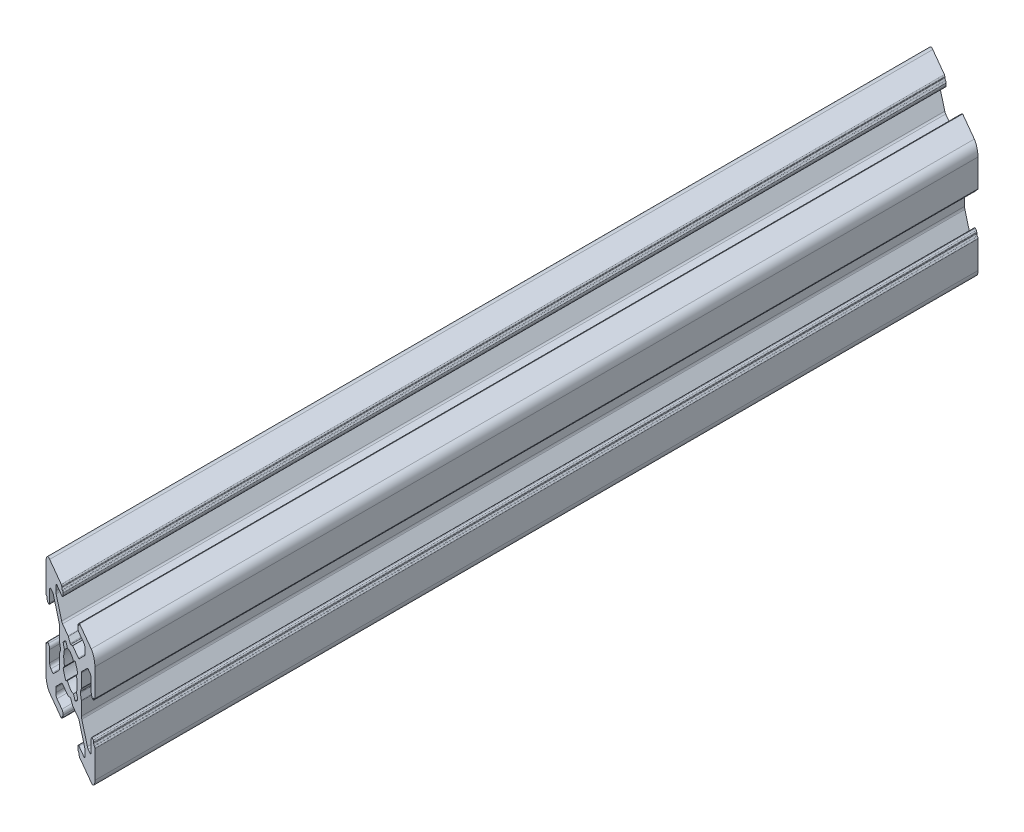
SolidWorks part; units mm, degrees
ref_plane "Front Plane" through (0, 0, 0) normal (0, 0, 1) x (1, 0, 0)
ref_plane "Top Plane" through (0, 0, 0) normal (0, 1, 0) x (1, 0, 0)
ref_plane "Right Plane" through (0, 0, 0) normal (1, 0, 0) x (0, 0, -1)
sketch "Sketch1" plane through (0, 0, 0) normal (0, 0, 1) x (1, 0, 0)
  line L0 (0, 13.3675) -> (0, -10.9159) construction
  line L1 (-12.9725, 0) -> (15.1887, 0) construction
  line L2 (-3.5, 8.5) -> (-5.5, 8.5)
  line L3 (-3.55, 9.7) -> (-3.55, 9.8)
  line L4 (-6, 7.2678) -> (-6, 8)
  line L5 (-7.2678, 6) -> (-8, 6)
  line L6 (-3.75, 10) -> (-8.5, 10)
  line L7 (-9.7, 3.55) -> (-9.8, 3.55)
  line L8 (-9.5, 3.2) -> (-9.5, 3.35)
  line L9 (-9, 3) -> (-9.3, 3)
  line L10 (-4.4732, 0.8536) -> (-4.0381, 0.1)
  line L11 (-4.5, 3.2322) -> (-4.5, 0.9536)
  line L12 (-8.5, 3.5) -> (-8.5, 5.5)
  line L13 (-10, 3.75) -> (-10, 8.5)
  line L14 (-3.5858, 4.6464) -> (-5.8536, 6.9142)
  line L15 (-4.6464, 3.5858) -> (-6.9142, 5.8536)
  line L16 (-3.2, 9.5) -> (-3.35, 9.5)
  line L17 (-3, 9) -> (-3, 9.3)
  line L18 (-0.8536, 4.4732) -> (-0.1, 4.0381)
  line L19 (-3.2322, 4.5) -> (-0.9536, 4.5)
  line L20 (-1.2582, 2.4453) -> (-1.9139, 2.9896)
  line L21 (-2.4453, 1.2582) -> (-2.9922, 1.9099)
  line L22 (3.5, -8.5) -> (5.5, -8.5)
  line L23 (3.55, -9.7) -> (3.55, -9.8)
  line L24 (6, -7.2678) -> (6, -8)
  line L25 (7.2678, -6) -> (8, -6)
  line L26 (3.75, -10) -> (8.5, -10)
  line L27 (9.7, -3.55) -> (9.8, -3.55)
  line L28 (9.5, -3.2) -> (9.5, -3.35)
  line L29 (9, -3) -> (9.3, -3)
  line L30 (4.4732, -0.8536) -> (4.0381, -0.1)
  line L31 (4.5, -3.2322) -> (4.5, -0.9536)
  line L32 (8.5, -3.5) -> (8.5, -5.5)
  line L33 (10, -3.75) -> (10, -8.5)
  line L34 (3.5858, -4.6464) -> (5.8536, -6.9142)
  line L35 (4.6464, -3.5858) -> (6.9142, -5.8536)
  line L36 (3.2, -9.5) -> (3.35, -9.5)
  line L37 (3, -9) -> (3, -9.3)
  line L38 (0.8536, -4.4732) -> (0.1, -4.0381)
  line L39 (3.2322, -4.5) -> (0.9536, -4.5)
  line L40 (1.2582, -2.4453) -> (1.9139, -2.9896)
  line L41 (2.4453, -1.2582) -> (2.9922, -1.9099)
  line L42 (-2.4453, -1.2582) -> (-2.9922, -1.9099)
  line L43 (-1.2582, -2.4453) -> (-1.9139, -2.9896)
  line L44 (-3.2322, -4.5) -> (-0.9536, -4.5)
  line L45 (-0.8536, -4.4732) -> (-0.1, -4.0381)
  line L46 (-3, -9) -> (-3, -9.3)
  line L47 (-3.2, -9.5) -> (-3.35, -9.5)
  line L48 (-4.6464, -3.5858) -> (-6.9142, -5.8536)
  line L49 (-3.5858, -4.6464) -> (-5.8536, -6.9142)
  line L50 (-10, -3.75) -> (-10, -8.5)
  line L51 (-8.5, -3.5) -> (-8.5, -5.5)
  line L52 (-4.5, -3.2322) -> (-4.5, -0.9536)
  line L53 (-4.4732, -0.8536) -> (-4.0381, -0.1)
  line L54 (-9, -3) -> (-9.3, -3)
  line L55 (-9.5, -3.2) -> (-9.5, -3.35)
  line L56 (-9.7, -3.55) -> (-9.8, -3.55)
  line L57 (2.4453, 1.2582) -> (2.9922, 1.9099)
  line L58 (1.2582, 2.4453) -> (1.9139, 2.9896)
  line L59 (3.2322, 4.5) -> (0.9536, 4.5)
  line L60 (0.8536, 4.4732) -> (0.1, 4.0381)
  line L61 (-3.75, -10) -> (-8.5, -10)
  line L62 (-7.2678, -6) -> (-8, -6)
  line L63 (-6, -7.2678) -> (-6, -8)
  line L64 (3, 9) -> (3, 9.3)
  line L65 (3.2, 9.5) -> (3.35, 9.5)
  line L66 (4.6464, 3.5858) -> (6.9142, 5.8536)
  line L67 (3.5858, 4.6464) -> (5.8536, 6.9142)
  line L68 (10, 3.75) -> (10, 8.5)
  line L69 (8.5, 3.5) -> (8.5, 5.5)
  line L70 (4.5, 3.2322) -> (4.5, 0.9536)
  line L71 (4.4732, 0.8536) -> (4.0381, 0.1)
  line L72 (9, 3) -> (9.3, 3)
  line L73 (9.5, 3.2) -> (9.5, 3.35)
  line L74 (9.7, 3.55) -> (9.8, 3.55)
  line L75 (3.75, 10) -> (8.5, 10)
  line L76 (7.2678, 6) -> (8, 6)
  line L77 (6, 7.2678) -> (6, 8)
  line L78 (3.55, 9.7) -> (3.55, 9.8)
  line L79 (3.5, 8.5) -> (5.5, 8.5)
  line L80 (-3.55, -9.7) -> (-3.55, -9.8)
  line L81 (-3.5, -8.5) -> (-5.5, -8.5)
  arc A0 (-10, 8.5) -> (-8.5, 10) centre (-8.5, 8.5) cw
  arc A1 (-8.5, 5.5) -> (-8, 6) centre (-8, 5.5) cw
  arc A2 (-7.2678, 6) -> (-6.9142, 5.8536) centre (-7.2678, 5.5) cw
  arc A3 (-5.8536, 6.9142) -> (-6, 7.2678) centre (-5.5, 7.2678) cw
  arc A4 (-6, 8) -> (-5.5, 8.5) centre (-5.5, 8) cw
  arc A5 (-9.7, 3.55) -> (-9.5, 3.35) centre (-9.7, 3.35) cw
  arc A6 (-9.8, 3.55) -> (-10, 3.75) centre (-9.8, 3.75) cw
  arc A7 (-9.3, 3) -> (-9.5, 3.2) centre (-9.3, 3.2) cw
  arc A8 (-8.5, 3.5) -> (-9, 3) centre (-9, 3.5) cw
  arc A9 (-4.6464, 3.5858) -> (-4.5, 3.2322) centre (-5, 3.2322) cw
  arc A10 (-4.4732, 0.8536) -> (-4.5, 0.9536) centre (-4.3, 0.9536) cw
  arc A11 (-4.0381, 0.1) -> (-4.0381, -0.1) centre (-4.2113, 0) cw
  arc A12 (-3.2, 9.5) -> (-3, 9.3) centre (-3.2, 9.3) cw
  arc A13 (-0.9536, 4.5) -> (-0.8536, 4.4732) centre (-0.9536, 4.3) cw
  arc A14 (-2.9922, 1.9099) -> (-1.9139, 2.9896) centre (0, 0) cw
  arc A15 (-3.2322, 4.5) -> (-3.5858, 4.6464) centre (-3.2322, 5) cw
  arc A16 (-3.75, 10) -> (-3.55, 9.8) centre (-3.75, 9.8) cw
  arc A17 (-3.35, 9.5) -> (-3.55, 9.7) centre (-3.35, 9.7) cw
  arc A18 (2.4453, -1.2582) -> (2.4453, 1.2582) centre (0, 0) ccw
  arc A19 (-3, 9) -> (-3.5, 8.5) centre (-3.5, 9) cw
  arc A20 (-2.4453, -1.2582) -> (-2.4453, 1.2582) centre (0, 0) cw
  arc A21 (10, -8.5) -> (8.5, -10) centre (8.5, -8.5) cw
  arc A22 (8.5, -5.5) -> (8, -6) centre (8, -5.5) cw
  arc A23 (7.2678, -6) -> (6.9142, -5.8536) centre (7.2678, -5.5) cw
  arc A24 (5.8536, -6.9142) -> (6, -7.2678) centre (5.5, -7.2678) cw
  arc A25 (6, -8) -> (5.5, -8.5) centre (5.5, -8) cw
  arc A26 (9.7, -3.55) -> (9.5, -3.35) centre (9.7, -3.35) cw
  arc A27 (9.8, -3.55) -> (10, -3.75) centre (9.8, -3.75) cw
  arc A28 (9.3, -3) -> (9.5, -3.2) centre (9.3, -3.2) cw
  arc A29 (8.5, -3.5) -> (9, -3) centre (9, -3.5) cw
  arc A30 (4.6464, -3.5858) -> (4.5, -3.2322) centre (5, -3.2322) cw
  arc A31 (4.4732, -0.8536) -> (4.5, -0.9536) centre (4.3, -0.9536) cw
  arc A32 (3.2, -9.5) -> (3, -9.3) centre (3.2, -9.3) cw
  arc A33 (-0.1, -4.0381) -> (0.1, -4.0381) centre (0, -4.2113) cw
  arc A34 (0.9536, -4.5) -> (0.8536, -4.4732) centre (0.9536, -4.3) cw
  arc A35 (2.9922, -1.9099) -> (1.9139, -2.9896) centre (0, 0) cw
  arc A36 (1.2582, -2.4453) -> (-1.2582, -2.4453) centre (0, 0) cw
  arc A37 (3.2322, -4.5) -> (3.5858, -4.6464) centre (3.2322, -5) cw
  arc A38 (3.75, -10) -> (3.55, -9.8) centre (3.75, -9.8) cw
  arc A39 (3.35, -9.5) -> (3.55, -9.7) centre (3.35, -9.7) cw
  arc A40 (3, -9) -> (3.5, -8.5) centre (3.5, -9) cw
  arc A41 (-3, -9) -> (-3.5, -8.5) centre (-3.5, -9) ccw
  arc A42 (-3.35, -9.5) -> (-3.55, -9.7) centre (-3.35, -9.7) ccw
  arc A43 (-3.75, -10) -> (-3.55, -9.8) centre (-3.75, -9.8) ccw
  arc A44 (-3.2322, -4.5) -> (-3.5858, -4.6464) centre (-3.2322, -5) ccw
  arc A45 (-2.9922, -1.9099) -> (-1.9139, -2.9896) centre (0, 0) ccw
  arc A46 (-0.9536, -4.5) -> (-0.8536, -4.4732) centre (-0.9536, -4.3) ccw
  arc A47 (-3.2, -9.5) -> (-3, -9.3) centre (-3.2, -9.3) ccw
  arc A48 (-4.4732, -0.8536) -> (-4.5, -0.9536) centre (-4.3, -0.9536) ccw
  arc A49 (3, 9) -> (3.5, 8.5) centre (3.5, 9) ccw
  arc A50 (3.35, 9.5) -> (3.55, 9.7) centre (3.35, 9.7) ccw
  arc A51 (3.75, 10) -> (3.55, 9.8) centre (3.75, 9.8) ccw
  arc A52 (3.2322, 4.5) -> (3.5858, 4.6464) centre (3.2322, 5) ccw
  arc A53 (1.2582, 2.4453) -> (-1.2582, 2.4453) centre (0, 0) ccw
  arc A54 (-4.6464, -3.5858) -> (-4.5, -3.2322) centre (-5, -3.2322) ccw
  arc A55 (-8.5, -3.5) -> (-9, -3) centre (-9, -3.5) ccw
  arc A56 (-9.3, -3) -> (-9.5, -3.2) centre (-9.3, -3.2) ccw
  arc A57 (-9.8, -3.55) -> (-10, -3.75) centre (-9.8, -3.75) ccw
  arc A58 (-9.7, -3.55) -> (-9.5, -3.35) centre (-9.7, -3.35) ccw
  arc A59 (-6, -8) -> (-5.5, -8.5) centre (-5.5, -8) ccw
  arc A60 (2.9922, 1.9099) -> (1.9139, 2.9896) centre (0, 0) ccw
  arc A61 (0.9536, 4.5) -> (0.8536, 4.4732) centre (0.9536, 4.3) ccw
  arc A62 (-0.1, 4.0381) -> (0.1, 4.0381) centre (0, 4.2113) ccw
  arc A63 (-5.8536, -6.9142) -> (-6, -7.2678) centre (-5.5, -7.2678) ccw
  arc A64 (-7.2678, -6) -> (-6.9142, -5.8536) centre (-7.2678, -5.5) ccw
  arc A65 (-8.5, -5.5) -> (-8, -6) centre (-8, -5.5) ccw
  arc A66 (-10, -8.5) -> (-8.5, -10) centre (-8.5, -8.5) ccw
  arc A67 (3.2, 9.5) -> (3, 9.3) centre (3.2, 9.3) ccw
  arc A68 (4.0381, 0.1) -> (4.0381, -0.1) centre (4.2113, 0) ccw
  arc A69 (4.4732, 0.8536) -> (4.5, 0.9536) centre (4.3, 0.9536) ccw
  arc A70 (4.6464, 3.5858) -> (4.5, 3.2322) centre (5, 3.2322) ccw
  arc A71 (8.5, 3.5) -> (9, 3) centre (9, 3.5) ccw
  arc A72 (9.3, 3) -> (9.5, 3.2) centre (9.3, 3.2) ccw
  arc A73 (9.8, 3.55) -> (10, 3.75) centre (9.8, 3.75) ccw
  arc A74 (9.7, 3.55) -> (9.5, 3.35) centre (9.7, 3.35) ccw
  arc A75 (6, 8) -> (5.5, 8.5) centre (5.5, 8) ccw
  arc A76 (5.8536, 6.9142) -> (6, 7.2678) centre (5.5, 7.2678) ccw
  arc A77 (7.2678, 6) -> (6.9142, 5.8536) centre (7.2678, 5.5) ccw
  arc A78 (8.5, 5.5) -> (8, 6) centre (8, 5.5) ccw
  arc A79 (10, 8.5) -> (8.5, 10) centre (8.5, 8.5) ccw
  dimension "D4" = 5.5
  dimension "D1" = 6
  dimension "D2" = 20
  dimension "D3" = 20
  dimension "D5" = 5.5
  dimension "D6" = 10
  dimension "D7" = 6
  dimension "D8" = 6
  dimension "D9" = 6
extrude "Extrude1" add sketch "Sketch1" along normal blind 200
sketch "Sketch2" plane through (0, 0, 0) normal (0, 1, 0) x (1, 0, 0)
  line L0 (-8.5, -100) -> (62.6875, -100) construction
  line L1 (-8.5, -200) -> (-8.5, 0) construction
  line L2 (0, 0) -> (0, -211.3787) construction
  line L3 (10, -29.4335) -> (-10, -17.8865)
  line L4 (10, -200) -> (10, 0) construction
  line L5 (-10, -200) -> (-10, 0) construction
  line L6 (-10, -17.8865) -> (-10, 13.957)
  line L7 (-10, 13.957) -> (10, 13.957)
  line L8 (10, 13.957) -> (10, -29.4335)
  line L9 (-10, -170.5665) -> (10, -182.1135)
  line L10 (10, -182.1135) -> (10, -215.5437)
  line L11 (10, -215.5437) -> (-10, -215.5437)
  line L12 (-10, -215.5437) -> (-10, -170.5665)
  point P15 (0, -23.66)
  point P18 (0, -176.34)
  dimension "D1" = 76.34
  dimension "D2" = 60
  dimension "D3" = 76.34
  dimension "D4" = 60
extrude "Cut-Extrude1" cut sketch "Sketch2" against normal through all and the other way through all
